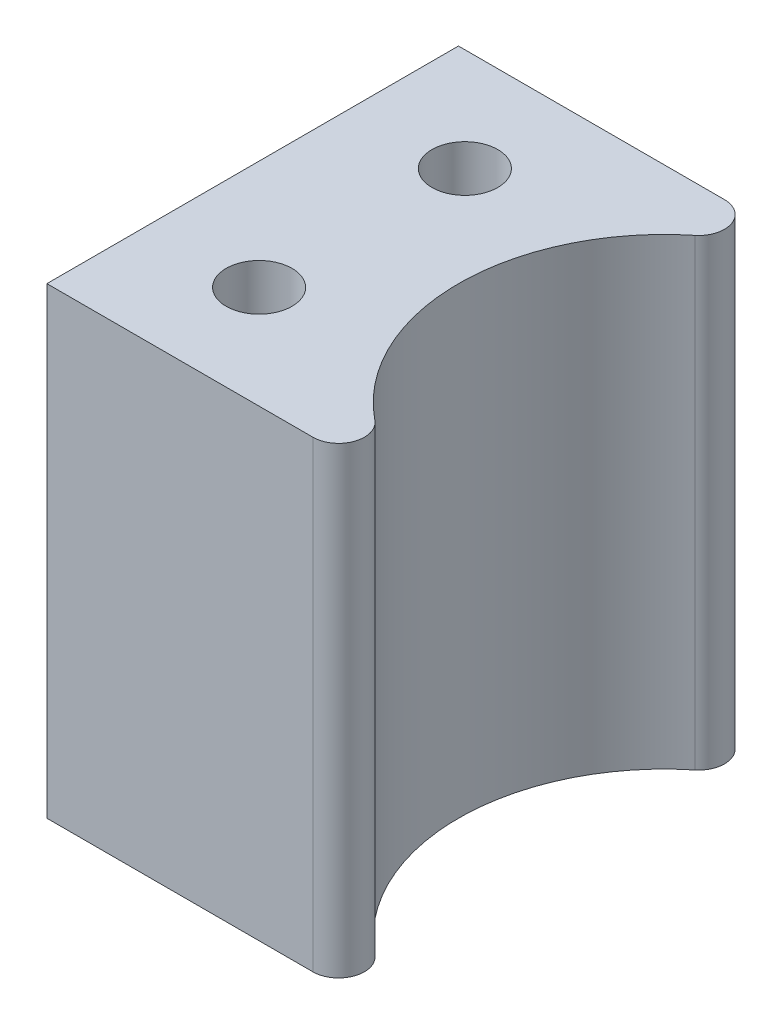
SolidWorks part; units mm, degrees
material "ABS"
ref_plane "Front Plane" through (0, 0, 0) normal (0, 0, 1) x (1, 0, 0)
ref_plane "Top Plane" through (0, 0, 0) normal (0, 1, 0) x (1, 0, 0)
ref_plane "Right Plane" through (0, 0, 0) normal (1, 0, 0) x (0, 0, -1)
sketch "Sketch3" plane through (0, 0, 0) normal (0, 1, 0) x (1, 0, 0)
  line L0 (-27.7812, 0) -> (-27.7812, 25.4)
  line L1 (-27.7812, 25.4) -> (-11.3615, 25.4)
  line L3 (-27.7812, 0) -> (-11.3615, 0)
  arc A0 (-11.3615, 0) -> (-10.3637, 2.8222) centre (-11.3615, 1.5875) ccw
  arc A1 (-11.3615, 25.4) -> (-10.3637, 22.5778) centre (-11.3615, 23.8125) cw
  arc A2 (-10.3637, 22.5778) -> (-10.3637, 2.8222) centre (-2.3813, 12.7) ccw
  circle A3 centre (-21.0344, 6.35) radius 2.032
  circle A4 centre (-21.0344, 19.05) radius 2.032
extrude "Boss-Extrude1" add sketch "Sketch3" along normal blind 28.575
